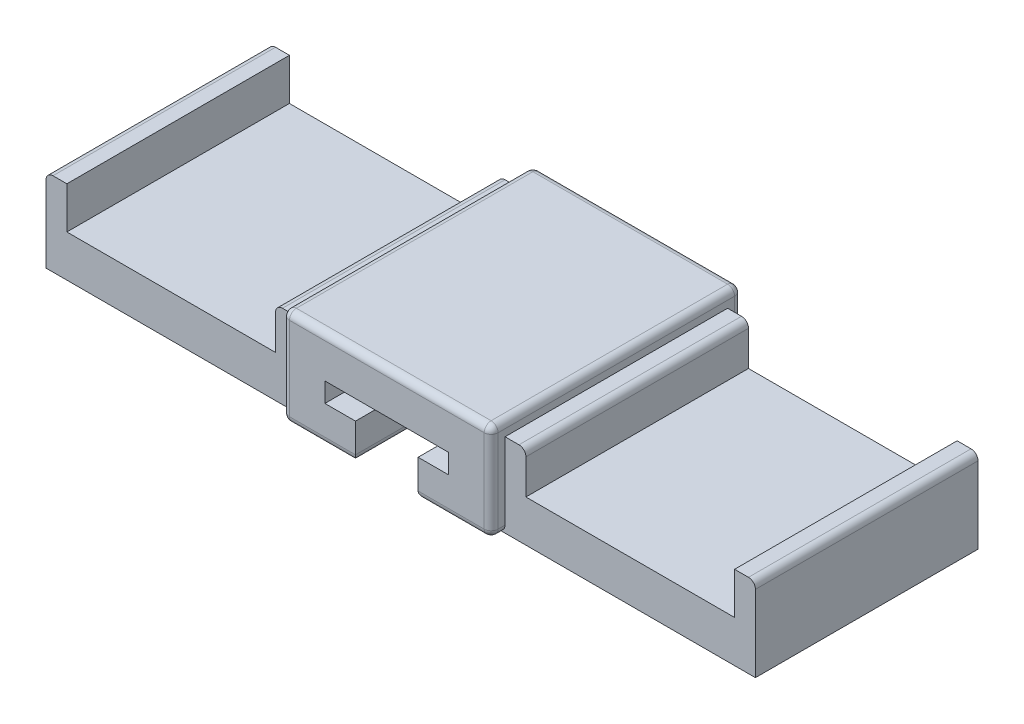
SolidWorks part; units mm, degrees
ref_plane "Front Plane" through (0, 0, 0) normal (0, 0, 1) x (1, 0, 0)
ref_plane "Top Plane" through (0, 0, 0) normal (0, 1, 0) x (1, 0, 0)
ref_plane "Right Plane" through (0, 0, 0) normal (1, 0, 0) x (0, 0, -1)
sketch "Sketch1" plane through (0, 0, 0) normal (0, 1, 0) x (1, 0, 0)
  line L1 (-7.5, -9) -> (7.5, -9)
  line L2 (-7.5, -9) -> (-7.5, 9)
  line L3 (-7.5, 9) -> (7.5, 9)
  line L4 (7.5, -9) -> (7.5, 9)
  line L5 (-7.5, -9) -> (7.5, 9) construction
  line L6 (-7.5, 9) -> (7.5, -9) construction
  point P0 (0, 0)
  dimension "D1" = 18
  dimension "D2" = 15
extrude "Boss-Extrude1" add sketch "Sketch1" along normal blind 7
sketch "Sketch2" plane through (0, 0, 9) normal (0, 0, 1) x (1, 0, 0)
  line L0 (-4.45, 0) -> (4.45, 0)
  line L1 (-7.5, 0) -> (7.5, 0) construction
  line L2 (4.45, 0) -> (4.45, 4)
  line L3 (4.45, 4) -> (-4.45, 4)
  line L4 (-4.45, 4) -> (-4.45, 0)
  line L5 (-4.45, 2.6) -> (4.45, 2.6)
  line L6 (-2.25, 2.6) -> (-2.25, 0)
  line L7 (0, 0) -> (0, 7) construction
  line L8 (-7.5, 7) -> (7.5, 7) construction
  line L9 (2.25, 2.6) -> (2.25, 0)
  line L10 (-0.6, 0) -> (-0.6, 5)
  line L11 (-0.6, 5) -> (0.6, 5)
  line L12 (0.6, 5) -> (0.6, 0)
  line L13 (1.1, 2.6) -> (1.1, 0)
  line L14 (-1.1, 2.6) -> (-1.1, 0)
  point P6 (0, 0)
  dimension "D1" = 4
  dimension "D2" = 1.4
  dimension "D3" = 4.5
  dimension "D4" = 1.2
  dimension "0.5" = 0.5
  dimension "D6" = 8.9
extrude "Cut-Extrude1" cut sketch "Sketch2" against normal blind 16.2 contours L5 L10 L3 L4 | L3 L12 L5 L2 | L5 L7 L3 L10 | L7 L5 L12 L3 | L14 L5 L6 L0 | L5 L14 L4 L10 | L4 L7 L5 L10 | L7 L0 L12 L5 | L13 L5 L12 L0 | L5 L13 L4 L9
sketch "Sketch8" plane through (0, 0, 9) normal (0, 0, 1) x (1, 0, 0)
  line L0 (-1.1, 2.6) -> (-0.6, 2.6)
  line L1 (-0.6, 2.6) -> (-0.6, 0)
  line L2 (-0.6, 0) -> (-1.1, 0)
  line L3 (-1.1, 0) -> (-1.1, 2.6)
  line L4 (0.6, 2.6) -> (1.1, 2.6)
  line L5 (1.1, 2.6) -> (1.1, 0)
  line L6 (1.1, 0) -> (0.6, 0)
  line L7 (0.6, 0) -> (0.6, 2.6)
sketch "Sketch9" plane through (-7.5, 0, 0) normal (-1, 0, 0) x (0, 0, 1)
  line L0 (-8, 0) -> (-8, 6)
  line L1 (9, 0) -> (-9, 0) construction
  line L2 (-8, 6) -> (8, 6)
  line L3 (8, 6) -> (8, 0)
  line L4 (-9, 0) -> (9, 0) construction
  line L5 (8, 0) -> (-8, 0)
  line L6 (-0.3093, 0) -> (0, 0) construction
  line L7 (0, 0) -> (0, 6) construction
  dimension "D1" = 16
  dimension "D2" = 6
extrude "Boss-Extrude2" add sketch "Sketch9" along normal blind 18
sketch "Sketch12" plane through (0, 0, 8) normal (0, 0, 1) x (1, 0, 0)
  line L0 (-16.5, 0) -> (-16.5, 6) construction
  line L1 (-25.5, 0) -> (-7.5, 0) construction
  line L2 (-25.5, 6) -> (-7.5, 6) construction
  dimension "D1" = 16.5
sketch "Sketch13" plane through (7.5, 0, 0) normal (1, 0, 0) x (0, 0, -1)
  line L0 (-8, 0) -> (-8, 6)
  line L1 (-8, 0) -> (-8, 6) construction
  line L2 (-8, 6) -> (8, 6)
  line L3 (8, 6) -> (8, 0)
  line L4 (9, 0) -> (-9, 0) construction
  line L5 (8, 0) -> (-8, 0)
  line L6 (0, 0) -> (0, 7) construction
  line L7 (-9, 0) -> (9, 0) construction
  line L8 (-9, 7) -> (9, 7) construction
  dimension "D2" = 6
extrude "Boss-Extrude3" add sketch "Sketch13" along normal blind 18
sketch "Sketch14" plane through (0, 0, 9) normal (0, 0, 1) x (1, 0, 0)
  line L0 (0, 0) -> (0, 7) construction
  line L1 (-7.5, 7) -> (7.5, 7) construction
  line L3 (25.5, 0) -> (7.5, 0) construction
  line L7 (16.5, 0) -> (16.5, 0.2814) construction
  line L12 (16.5, 0) -> (16.5, 6) construction
  line L13 (25.5, 6) -> (7.5, 6) construction
  line L17 (9, 6) -> (9, 3)
  line L18 (9, 3) -> (24, 3)
  line L19 (24, 3) -> (24, 6)
  line L20 (24, 6) -> (9, 6)
  line L23 (-24, 3) -> (-24, 6)
  line L24 (-9, 3) -> (-24, 3)
  line L25 (-9, 6) -> (-9, 3)
  line L30 (-24, 6) -> (-9, 6)
  dimension "D1" = 15
  dimension "D2" = 3
extrude "Cut-Extrude5" cut sketch "Sketch14" against normal blind 32.55
fillet "Fillet1" radius 0.5 21 edges at (0, 0, -9) (0, 7, -9) (7.5, 0, -8.5) (-7.5, 0, -8.5) (-7.5, 0, 8.5) (7.5, 0, 8.5) (7.5, 7, 0) (25.5, 6, 0) (-25.5, 6, 0) (-7.5, 7, 0) (-7.5, 3.5, 9) (7.5, 3.5, 9) (4.875, 0, 9) (2.25, 0, 0.9) (-2.25, 0, 0.9) (-4.875, 0, 9) (0, 7, 9) (7.5, 3.5, -9) (-7.5, 3.5, -9) (-9, 6, 0) (9, 6, 0)
